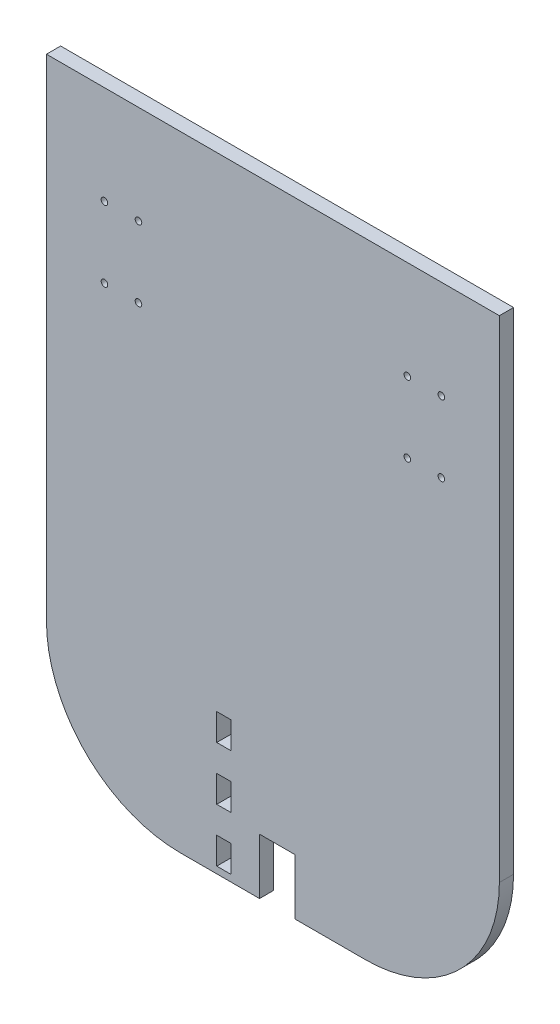
SolidWorks part; units mm, degrees
ref_plane "Front" through (0, 0, 0) normal (0, 0, 1) x (1, 0, 0)
ref_plane "Top" through (0, 0, 0) normal (0, 1, 0) x (1, 0, 0)
ref_plane "Right" through (0, 0, 0) normal (1, 0, 0) x (0, 0, -1)
sketch "Sketch1" plane through (0, 0, 0) normal (0, 0, 1) x (1, 0, 0)
  line L1 (-101.5, -140) -> (101.5, -140)
  line L2 (-101.5, -140) -> (-101.5, 140)
  line L3 (-101.5, 140) -> (101.5, 140)
  line L4 (101.5, -140) -> (101.5, 140)
  line L5 (-101.5, -140) -> (101.5, 140) construction
  line L6 (-101.5, 140) -> (101.5, -140) construction
  point P0 (0, 0)
  dimension "D1" = 203
  dimension "D2" = 280
extrude "Boss-Extrude1" add sketch "Sketch1" along normal blind 6.35
sketch "Sketch2" plane through (0, 0, 6.35) normal (0, 0, 1) x (1, 0, 0)
  line L0 (-101.5, 80) -> (101.5, 80) construction
  line L1 (-101.5, 140) -> (-101.5, -140) construction
  line L2 (101.5, -140) -> (101.5, 140) construction
  line L3 (0, 0) -> (0, 140) construction
  line L4 (101.5, 140) -> (-101.5, 140) construction
  line L5 (-101.5, 0) -> (101.5, 0) construction
  line L6 (-60.26, 95.875) -> (-75.5, 64.125) construction
  line L7 (60.26, 64.125) -> (75.5, 64.125) construction
  line L8 (60.26, 64.125) -> (60.26, 95.875) construction
  line L9 (60.26, 95.875) -> (75.5, 95.875) construction
  line L10 (75.5, 64.125) -> (75.5, 95.875) construction
  line L11 (60.26, 64.125) -> (75.5, 95.875) construction
  line L12 (60.26, 95.875) -> (75.5, 64.125) construction
  line L13 (-60.26, 64.125) -> (-75.5, 95.875) construction
  line L14 (-75.5, 64.125) -> (-75.5, 95.875) construction
  line L15 (-60.26, 95.875) -> (-75.5, 95.875) construction
  line L16 (-60.26, 64.125) -> (-60.26, 95.875) construction
  line L17 (-60.26, 64.125) -> (-75.5, 64.125) construction
  circle A0 centre (60.26, 95.875) radius 1.475
  circle A1 centre (75.5, 95.875) radius 1.475
  circle A2 centre (60.26, 64.125) radius 1.475
  circle A3 centre (75.5, 64.125) radius 1.475
  circle A4 centre (-75.5, 64.125) radius 1.475
  circle A5 centre (-60.26, 64.125) radius 1.475
  circle A6 centre (-75.5, 95.875) radius 1.475
  circle A7 centre (-60.26, 95.875) radius 1.475
  point P13 (67.88, 80)
  point P30 (-67.88, 80)
  dimension "D1" = 2.95
  dimension "D2" = 15.24
  dimension "D3" = 31.75
  dimension "D4" = 60
  dimension "D5" = 26
extrude "Cut-Extrude1" cut sketch "Sketch2" against normal up to surface (6.35 mm away) up to face at (0, 0, 0)
sketch "Sketch3" plane through (0, 0, 6.35) normal (0, 0, 1) x (1, 0, 0)
  line L0 (0, 0) -> (0, -140) construction
  line L1 (-101.5, -140) -> (101.5, -140) construction
  line L2 (0, 0) -> (-101.5, 0) construction
  line L3 (-101.5, 140) -> (-101.5, -140) construction
  line L4 (-22, -140) -> (-22, 0) construction
  line L5 (2, 0) -> (2, -140) construction
  line L6 (-18.825, -125) -> (-25.175, -125)
  line L7 (-18.825, -125) -> (-18.825, -137)
  line L8 (-18.825, -137) -> (-25.175, -137)
  line L9 (-25.175, -125) -> (-25.175, -137)
  line L10 (-18.825, -125) -> (-25.175, -137) construction
  line L11 (-18.825, -137) -> (-25.175, -125) construction
  line L12 (-25.175, -101) -> (-18.825, -101)
  line L13 (-25.175, -101) -> (-25.175, -113)
  line L14 (-25.175, -113) -> (-18.825, -113)
  line L15 (-18.825, -101) -> (-18.825, -113)
  line L16 (-25.175, -101) -> (-18.825, -113) construction
  line L17 (-25.175, -113) -> (-18.825, -101) construction
  line L18 (-25.175, -77) -> (-18.825, -77)
  line L19 (-25.175, -77) -> (-25.175, -89)
  line L20 (-25.175, -89) -> (-18.825, -89)
  line L21 (-18.825, -77) -> (-18.825, -89)
  line L22 (-25.175, -77) -> (-18.825, -89) construction
  line L23 (-25.175, -89) -> (-18.825, -77) construction
  line L25 (-6, -115) -> (10, -115)
  line L26 (-6, -115) -> (-6, -140)
  line L27 (-6, -140) -> (10, -140)
  line L28 (10, -115) -> (10, -140)
  line L29 (-6, -115) -> (10, -140) construction
  line L30 (-6, -140) -> (10, -115) construction
  point P10 (-22, -131)
  point P15 (-22, -107)
  point P20 (-22, -83)
  point P27 (2, -127.5)
  dimension "D1" = 12
  dimension "D2" = 6.35
  dimension "D3" = 3
  dimension "D4" = 12
  dimension "D5" = 12
  dimension "D6" = 22
  dimension "D7" = 25
  dimension "D8" = 16
  dimension "D9" = 2
extrude "Cut-Extrude2" cut sketch "Sketch3" against normal up to surface (6.35 mm away) up to face at (-61.735, 95.875, 0)
fillet "Fillet1" radius 60 2 edges at (101.5, -140, 3.175) (-101.5, -140, 3.175)
